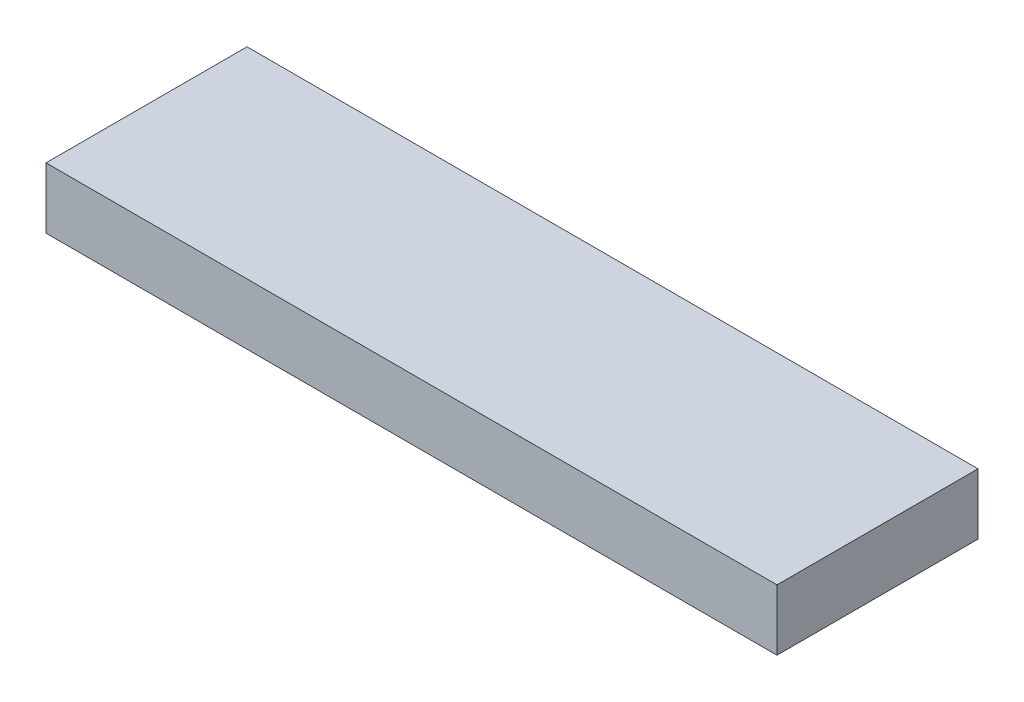
SolidWorks part; units mm, degrees
ref_plane "Plane1" through (0, 0, 0) normal (0, 0, 1) x (1, 0, 0)
ref_plane "Plane2" through (0, 0, 0) normal (0, 1, 0) x (1, 0, 0)
ref_plane "Plane3" through (0, 0, 0) normal (1, 0, 0) x (0, 0, -1)
sketch "Sketch2" plane through (0, 0, 0) normal (0, 1, 0) x (1, 0, 0)
  line L1 (0, 0) -> (120, 0)
  line L2 (0, 0) -> (0, 33)
  line L3 (0, 33) -> (120, 33)
  line L4 (120, 0) -> (120, 33)
  dimension "D1" = 33
  dimension "D2" = 120
extrude "Boss-Extrude1" add sketch "Sketch2" along normal blind 10
